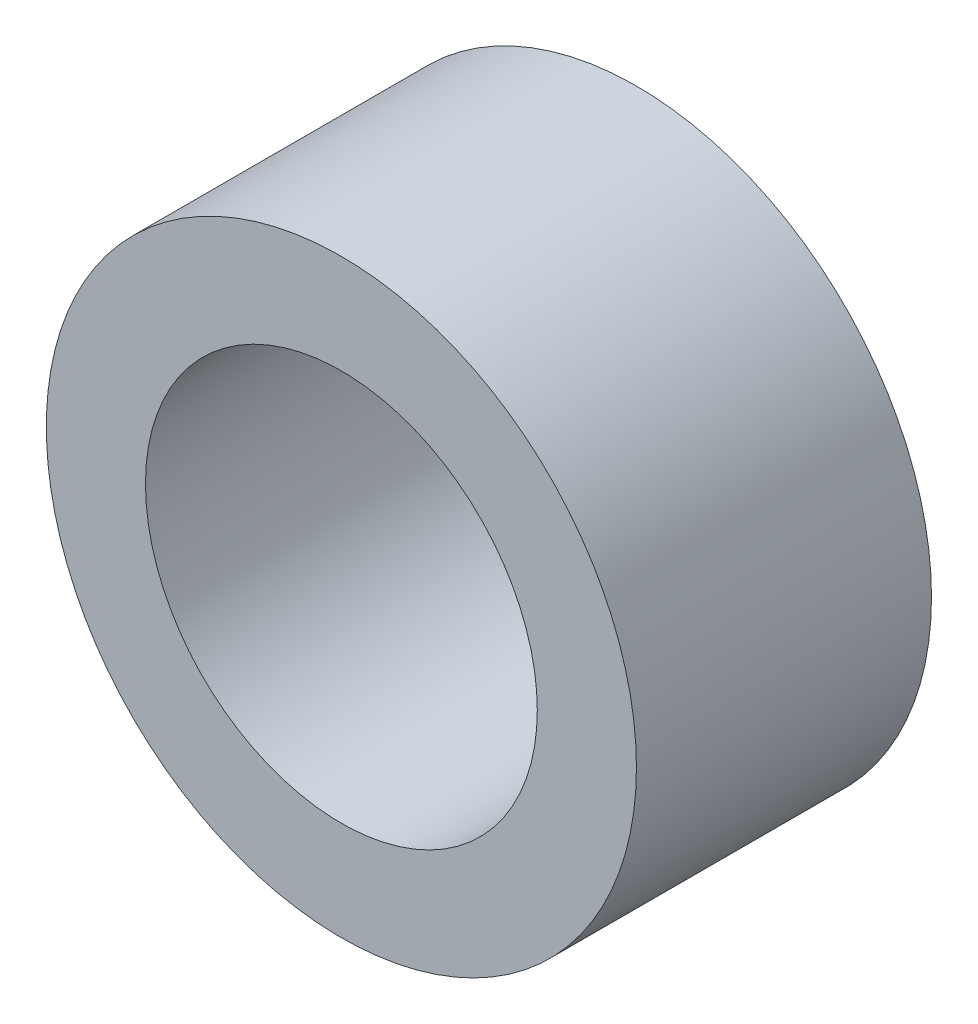
SolidWorks part; units mm, degrees
ref_plane "Front Plane" through (0, 0, 0) normal (0, 0, 1) x (1, 0, 0)
ref_plane "Top Plane" through (0, 0, 0) normal (0, 1, 0) x (1, 0, 0)
ref_plane "Right Plane" through (0, 0, 0) normal (1, 0, 0) x (0, 0, -1)
sketch "Sketch1" plane through (0, 0, 0) normal (0, 0, 1) x (1, 0, 0)
  circle A0 centre (0, 0) radius 3.175
  circle A1 centre (0, 0) radius 2.1082
  dimension "OD" = 6.35
  dimension "ID" = 4.2164
extrude "Extrude1" add sketch "Sketch1" along normal mid plane 3.175
sketch "Sketch2" plane through (0, 0, 0) normal (1, 0, 0) x (0, 0, -1)
  line L0 (-1.5875, -2.1082) -> (1.5875, -2.1082) construction
  line L3 (1.5875, 2.1082) -> (-1.5875, 2.1082) construction
  line L5 (-1.5875, -2.1082) -> (1.5875, -2.1082)
  line L6 (1.5875, 2.1082) -> (-1.5875, 2.1082)
sketch "Sketch4" plane through (0, 0, 1.5875) normal (0, 0, 1) x (1, 0, 0)
  line L0 (0, 0) -> (-1.4907, 1.4907)
  line L1 (0, -1.7463) -> (0, 1.7463) construction
  circle A0 centre (0, 0) radius 2.1082 construction
  dimension "D1" = 45
